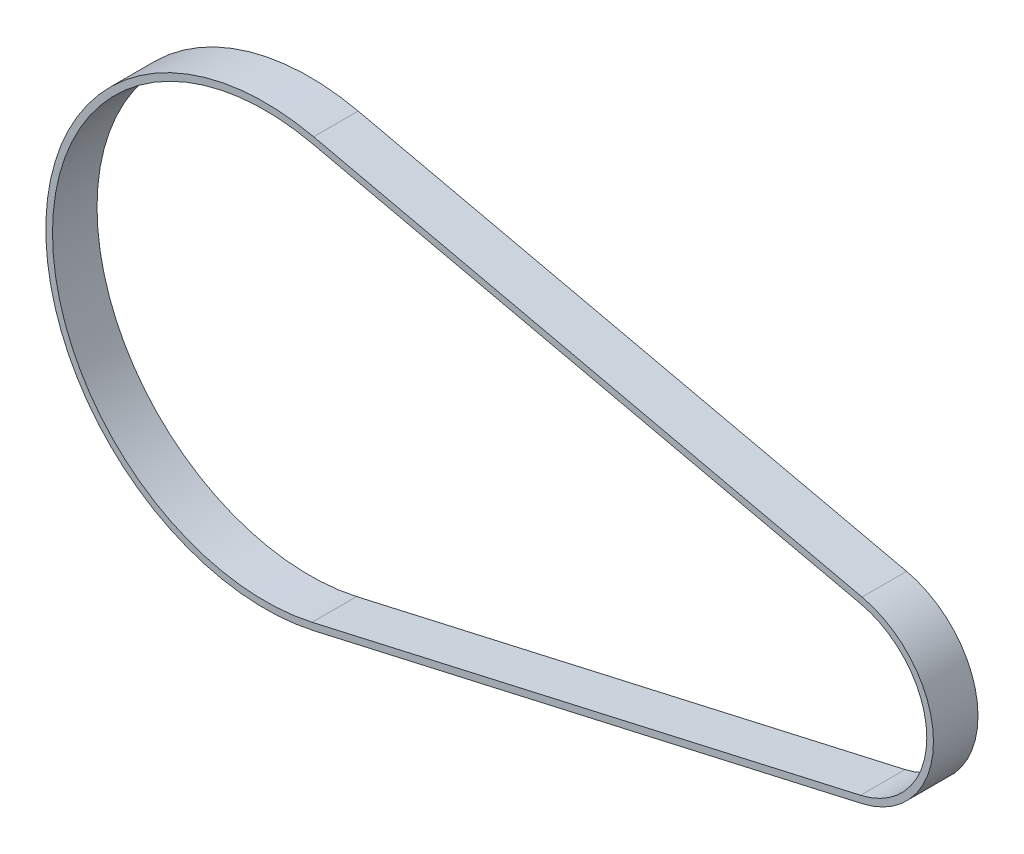
SolidWorks part; units mm, degrees
ref_plane "前基準面" through (0, 0, 0) normal (0, 0, 1) x (1, 0, 0)
ref_plane "上基準面" through (0, 0, 0) normal (0, 1, 0) x (1, 0, 0)
ref_plane "右基準面" through (0, 0, 0) normal (1, 0, 0) x (0, 0, -1)
sketch "草圖1" plane through (0, 0, 0) normal (0, 0, 1) x (1, 0, 0)
  line L0 (-64.75, 0) -> (64.75, 0) construction
  line L1 (-54.189, 46.5623) -> (68.9749, 18.6269)
  line L2 (-54.189, -46.5623) -> (68.9749, -18.6269)
  line L3 (-54.189, 46.5623) -> (-64.75, 0) construction
  line L4 (-64.75, 0) -> (-54.189, -46.5623) construction
  line L5 (68.9749, 18.6269) -> (64.75, 0) construction
  line L6 (64.75, 0) -> (68.9749, -18.6269) construction
  line L7 (-53.8572, 48.0252) -> (69.3067, 20.0897)
  line L8 (-53.8572, -48.0252) -> (69.3067, -20.0897)
  arc A0 (68.9749, -18.6269) -> (68.9749, 18.6269) centre (64.75, 0) ccw
  arc A1 (-54.189, 46.5623) -> (-54.189, -46.5623) centre (-64.75, 0) ccw
  arc A2 (69.3067, -20.0897) -> (69.3067, 20.0897) centre (64.75, 0) ccw
  arc A3 (-53.8572, 48.0252) -> (-53.8572, -48.0252) centre (-64.75, 0) ccw
  dimension "D2" = 38.2
  dimension "D3" = 95.49
  dimension "D1" = 129.5
  dimension "D4" = 205.559
  dimension "D5" = 154.441
  dimension "D6" = 126.2922
  dimension "D8" = 1.5
extrude "伸長1" add sketch "草圖1" along normal blind 10
